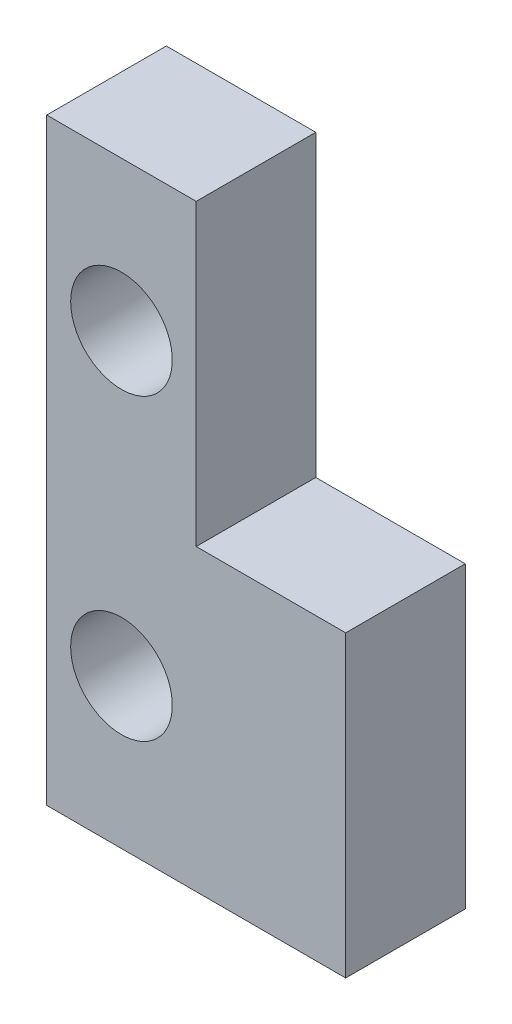
SolidWorks part; units mm, degrees
ref_plane "Plan de face" through (0, 0, 0) normal (0, 0, 1) x (1, 0, 0)
ref_plane "Plan de dessus" through (0, 0, 0) normal (0, 1, 0) x (1, 0, 0)
ref_plane "Plan de droite" through (0, 0, 0) normal (1, 0, 0) x (0, 0, -1)
sketch "Esquisse1" plane through (0, 0, 0) normal (0, 0, 1) x (1, 0, 0)
  line L1 (-5, 10) -> (5, 10)
  line L2 (-5, 10) -> (-5, -10)
  line L3 (-5, -10) -> (5, -10)
  line L4 (5, 10) -> (5, -10)
  line L5 (-5, 10) -> (5, -10) construction
  line L6 (-5, -10) -> (5, 10) construction
  point P0 (0, 0)
  dimension "D1" = 10
  dimension "D2" = 20
extrude "Boss.-Extru.1" add sketch "Esquisse1" along normal blind 4
sketch "Esquisse2" plane through (0, 0, 0) normal (0, 0, -1) x (-1, 0, 0)
  line L1 (-5, 10) -> (0, 10)
  line L2 (-5, 10) -> (-5, 0)
  line L3 (-5, 0) -> (0, 0)
  line L4 (0, 10) -> (0, 0)
sketch "Esquisse6" plane through (0, 0, 0) normal (0, 0, -1) x (-1, 0, 0)
  line L0 (0, 10) -> (5, 10) construction
  line L1 (5, 10) -> (2.5, 10) construction
  line L2 (2.5, 10) -> (2.5, -10) construction
  line L3 (5, -10) -> (-5, -10) construction
  line L4 (2.5, -10) -> (2.5, 0) construction
  line L5 (2.5, 0) -> (2.5, -5) construction
  line L6 (2.5, -5) -> (2.5, 5) construction
hole_wizard "Dégagement M33" positions "Esquisse9" profile "Esquisse10" hole size "M3" standard "ISO" end condition through all
sketch "Esquisse9" plane through (0, 0, 0) normal (0, 0, -1) x (-1, 0, 0)
  point P0 (2.5, 5)
  point P3 (2.5, -5)
sketch "Esquisse10" plane through (-2.5, 5, 0) normal (1, 0, 0) x (0, 1, 0)
  line L0 (0, 0) -> (0, 4)
  line L1 (0, 4) -> (1.7, 4)
  line L2 (1.7, 4) -> (1.7, 0)
  line L5 (1.7, 0) -> (0, 0)
  line L11 (0, -6.35) -> (0, 107.95) construction
  dimension "Diamètre du perçage jusqu'au prochain" = 3.4
  dimension "Profondeur du perçage jusqu'au prochain" = 4
extrude "Enlèv. mat.-Extru.2" cut sketch "Esquisse2" against normal blind 4
